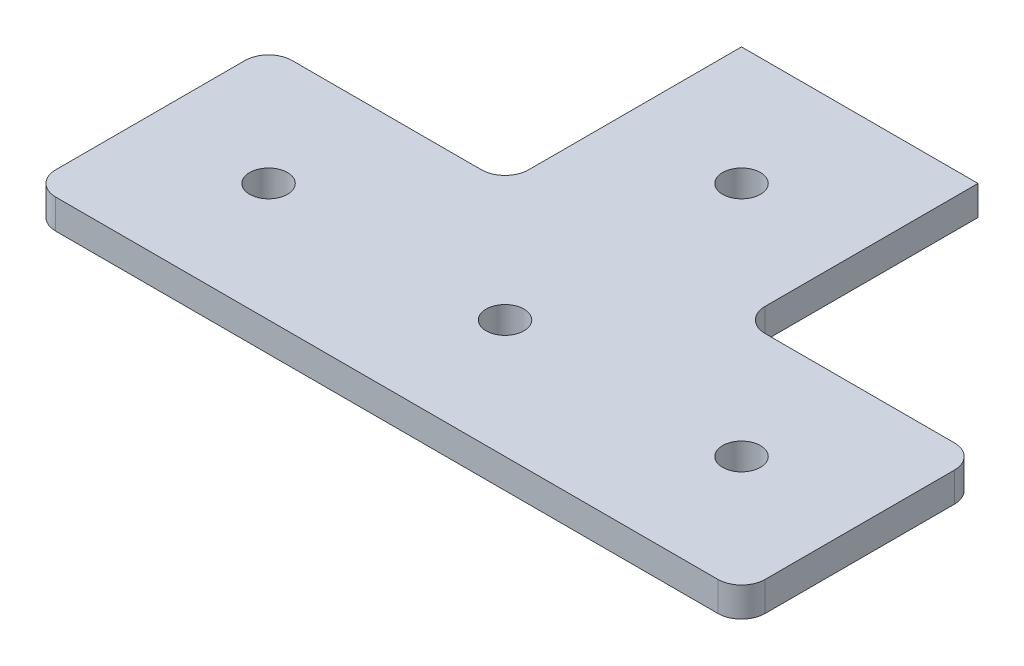
SolidWorks part; units mm, degrees
material "3.0205 (EN-AW 1200)"
ref_plane "Front Plane" through (0, 0, 0) normal (0, 0, 1) x (1, 0, 0)
ref_plane "Top Plane" through (0, 0, 0) normal (0, 1, 0) x (1, 0, 0)
ref_plane "Right Plane" through (0, 0, 0) normal (1, 0, 0) x (0, 0, -1)
sketch "Sketch1" plane through (0, 0, 0) normal (0, 1, 0) x (1, 0, 0)
  line L0 (18.7205, 17.4957) -> (39.0405, 17.4957)
  line L1 (-32.0795, 17.4957) -> (-11.7595, 17.4957)
  line L2 (-34.6195, 14.9557) -> (-34.6195, -5.3643)
  line L3 (-32.0795, -7.9043) -> (39.0405, -7.9043)
  line L4 (41.5805, 14.9557) -> (41.5805, -5.3643)
  line L10 (-9.2195, 20.0357) -> (-9.2195, 42.8957)
  line L12 (16.1805, 20.0357) -> (16.1805, 42.8957)
  line L13 (-9.2195, 42.8957) -> (16.1805, 42.8957)
  circle A0 centre (3.4805, 4.7957) radius 2.032
  circle A1 centre (-21.9195, 4.7957) radius 2.032
  circle A2 centre (28.8805, 4.7957) radius 2.032
  circle A3 centre (3.4805, 30.1957) radius 2.032
  arc A7 (-11.7595, 17.4957) -> (-9.2195, 20.0357) centre (-11.7595, 20.0357) ccw
  arc A8 (16.1805, 20.0357) -> (18.7205, 17.4957) centre (18.7205, 20.0357) ccw
  arc A9 (39.0405, 17.4957) -> (41.5805, 14.9557) centre (39.0405, 14.9557) cw
  arc A10 (41.5805, -5.3643) -> (39.0405, -7.9043) centre (39.0405, -5.3643) cw
  arc A11 (-32.0795, -7.9043) -> (-34.6195, -5.3643) centre (-32.0795, -5.3643) cw
  arc A12 (-34.6195, 14.9557) -> (-32.0795, 17.4957) centre (-32.0795, 14.9557) cw
  point P20 (16.1805, 68.2957)
  point P23 (-9.2195, 68.2957)
  point P28 (16.1805, 17.4957)
  point P31 (41.5805, 17.4957)
  point P34 (41.5805, -7.9043)
  point P37 (-34.6195, -7.9043)
  dimension "D6" = 4.064
  dimension "D7" = 12.7
  dimension "D8" = 12.7
  dimension "D9" = 4.064
  dimension "D10" = 4.064
  dimension "D11" = 12.7
  dimension "D12" = 25.4
  dimension "D13" = 25.4
  dimension "D14" = 12.7
  dimension "D15" = 4.064
  dimension "D16" = 25.4
  dimension "D17" = 12.7
  dimension "D21" = 12.7
  dimension "D1" = 76.2
  dimension "D2" = 25.4
  dimension "D3" = 50.8
  dimension "D4" = 25.4
  dimension "D5" = 25.4
extrude "Boss-Extrude1" add sketch "Sketch1" along normal blind 3.175
